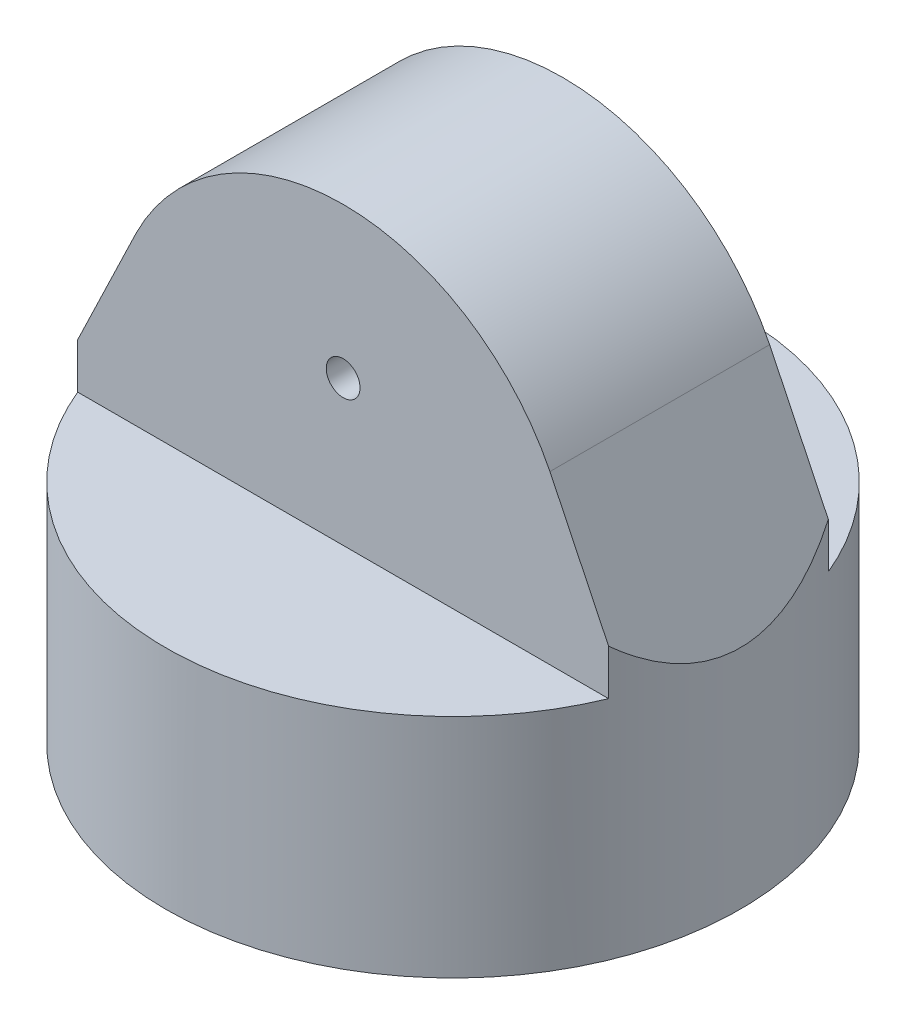
SolidWorks part; units mm, degrees
ref_plane "Front Plane" through (0, 0, 0) normal (0, 0, 1) x (1, 0, 0)
ref_plane "Top Plane" through (0, 0, 0) normal (0, 1, 0) x (1, 0, 0)
ref_plane "Right Plane" through (0, 0, 0) normal (1, 0, 0) x (0, 0, -1)
sketch "Sketch1" plane through (0, 0, 0) normal (0, 1, 0) x (1, 0, 0)
  circle A0 centre (0, 0) radius 85
  circle A1 centre (0, 0) radius 75
extrude "Boss-Extrude1" add sketch "Sketch1" along normal blind 35
sketch "Sketch2" plane through (0, 35, 0) normal (0, 1, 0) x (1, 0, 0)
  circle A0 centre (0, 0) radius 85
extrude "Boss-Extrude2" add sketch "Sketch2" along normal blind 4
sketch "Sketch3" plane through (0, 0, 0) normal (0, 0, 1) x (1, 0, 0)
  line L0 (-85, 39) -> (-61.181, 88.5127)
  line L1 (-85, 39) -> (85, 39)
  line L2 (85, 39) -> (61.181, 88.5127)
  arc A0 (-61.181, 88.5127) -> (61.181, 88.5127) centre (0, 58.0346) cw
  circle A1 centre (0, 81.8442) radius 5
extrude "Boss-Extrude3" add sketch "Sketch3" along normal mid plane 65
sketch "Sketch4" plane through (0, 39, 0) normal (0, 1, 0) x (1, 0, 0)
  circle A0 centre (0, 0) radius 85
  circle A1 centre (0, 0) radius 95.7387
extrude "Cut-Extrude1" cut sketch "Sketch4" along normal blind 67
sketch "Sketch5" plane through (0, 35, 0) normal (0, -1, 0) x (1, 0, 0)
  line L1 (-15.1, -17.6) -> (15.1, -17.6)
  line L2 (-17.6, -15.1) -> (-17.6, 15.1)
  line L3 (-15.1, 17.6) -> (15.1, 17.6)
  line L4 (17.6, -15.1) -> (17.6, 15.1)
  line L5 (-16.8678, -16.8678) -> (16.8678, 16.8678) construction
  line L6 (-16.8678, 16.8678) -> (16.8678, -16.8678) construction
  arc A1 (15.1, 17.6) -> (17.6, 15.1) centre (15.1, 15.1) cw
  arc A2 (15.1, -17.6) -> (17.6, -15.1) centre (15.1, -15.1) ccw
  arc A3 (-15.1, -17.6) -> (-17.6, -15.1) centre (-15.1, -15.1) cw
  arc A4 (-17.6, 15.1) -> (-15.1, 17.6) centre (-15.1, 15.1) cw
  dimension "D1" = 2.5
extrude "Cut-Extrude2" cut sketch "Sketch5" against normal blind 58
sketch "Sketch6" plane through (0, 0, 0) normal (0, -1, 0) x (1, 0, 0)
  circle A0 centre (0, 0) radius 75
  circle A1 centre (0, 0) radius 85
extrude "Boss-Extrude4" add sketch "Sketch6" along normal blind 28
